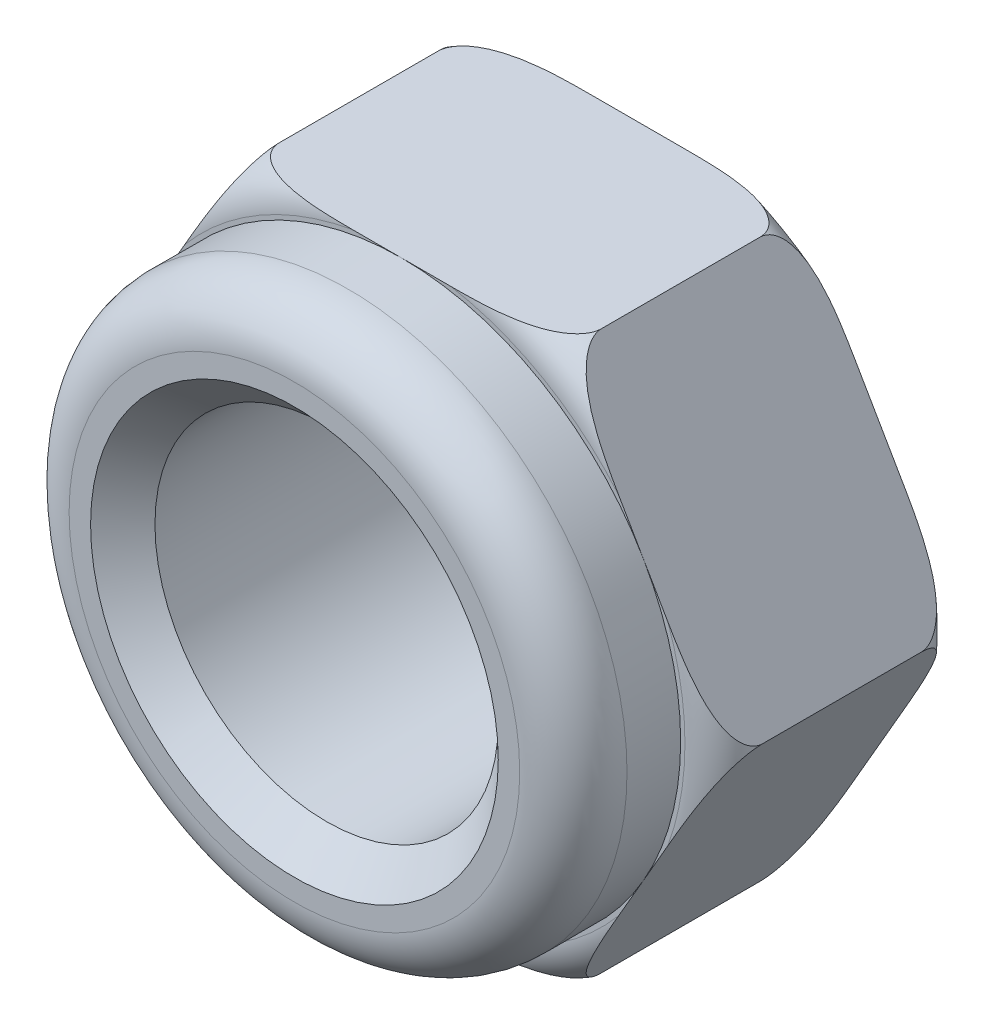
SolidWorks part; units mm, degrees
material "Stal węglowa"
ref_plane "Płaszczyzna XY" through (0, 0, 0) normal (0, 0, 1) x (1, 0, 0)
ref_plane "Płaszczyzna XZ" through (0, 0, 0) normal (0, 1, 0) x (1, 0, 0)
ref_plane "Płaszczyzna YZ" through (0, 0, 0) normal (1, 0, 0) x (0, 0, -1)
sketch "Szkic1" plane through (0, 0, 0) normal (0, 0, 1) x (1, 0, 0)
  line L1 (-7.5056, 0) -> (-3.7528, -6.5)
  line L2 (-3.7528, -6.5) -> (3.7528, -6.5)
  line L3 (3.7528, -6.5) -> (7.5056, 0)
  line L4 (7.5056, 0) -> (3.7528, 6.5)
  line L5 (3.7528, 6.5) -> (-3.7528, 6.5)
  line L6 (-3.7528, 6.5) -> (-7.5056, 0)
  circle A0 centre (0, 0) radius 6.5 construction
  circle A1 centre (0, 0) radius 4
  dimension "d" = 8
  dimension "s" = 13
extrude "Dodanie-wyciągnięcie1" add sketch "Szkic1" along normal blind 5.5
sketch "Szkic2" plane through (0, 0, 0) normal (0, 0, 1) x (1, 0, 0)
  line L0 (-3.7528, 6.5) -> (-7.5056, 0) construction
  circle A0 centre (0, 0) radius 4
  circle A1 centre (0, 0) radius 6.5
  circle A2 centre (0, 0) radius 4 construction
extrude "Dodanie-wyciągnięcie2" add sketch "Szkic2" along normal blind 8
chamfer "Sfazowanie1" distance 0.75 angle 45 2 edges at (4, 0, 8) (4, 0, 0)
sketch "Szkic3" plane through (0, 0, 0) normal (0, 1, 0) x (1, 0, 0)
  line L0 (-7.5056, -0.9056) -> (-7.5056, -4.5944)
  line L1 (-6.6, -5.5) -> (-3.7528, -5.5)
  line L2 (-6.6, 0) -> (-3.7528, 0)
  line L3 (0, 1.7016) -> (0, -9.3871) construction
  line L4 (-3.7528, -5.5) -> (-3.7528, 0)
  line L5 (-6.6, 0) -> (-7.5056, 0)
  line L6 (-7.5056, 0) -> (-7.5056, -5.5)
  line L7 (-7.5056, -5.5) -> (-6.6, -5.5)
  line L8 (-6.5, -5.5) -> (-5.6292, -5.5) construction
  line L9 (-6.5, -8) -> (6.5, -8) construction
  line L10 (-7.5056, -5.5) -> (-5.6292, -5.5) construction
  line L11 (-6.5, -5.5) -> (-6.5, -8) construction
  line L12 (-6.5, -5.5) -> (-6.5, -8) construction
  line L13 (-6.5, -6.75) -> (-6.5, -8)
  line L14 (-6.5, -8) -> (-5.25, -8)
  arc A0 (-7.5056, -4.5944) -> (-6.6, -5.5) centre (-6.6, -4.5944) ccw
  arc A1 (-7.5056, -0.9056) -> (-6.6, 0) centre (-6.6, -0.9056) cw
  arc A2 (-5.25, -8) -> (-6.5, -6.75) centre (-5.25, -6.75) cw
  point P13 (-7.5056, -5.5)
  point P16 (-7.5056, 0)
  dimension "D1" = 0.1
  dimension "D2" = 0.5
revolve "Wycięcie-obrót1" cut sketch "Szkic3" angle 360 about L3
equation "\"d\"=5"
